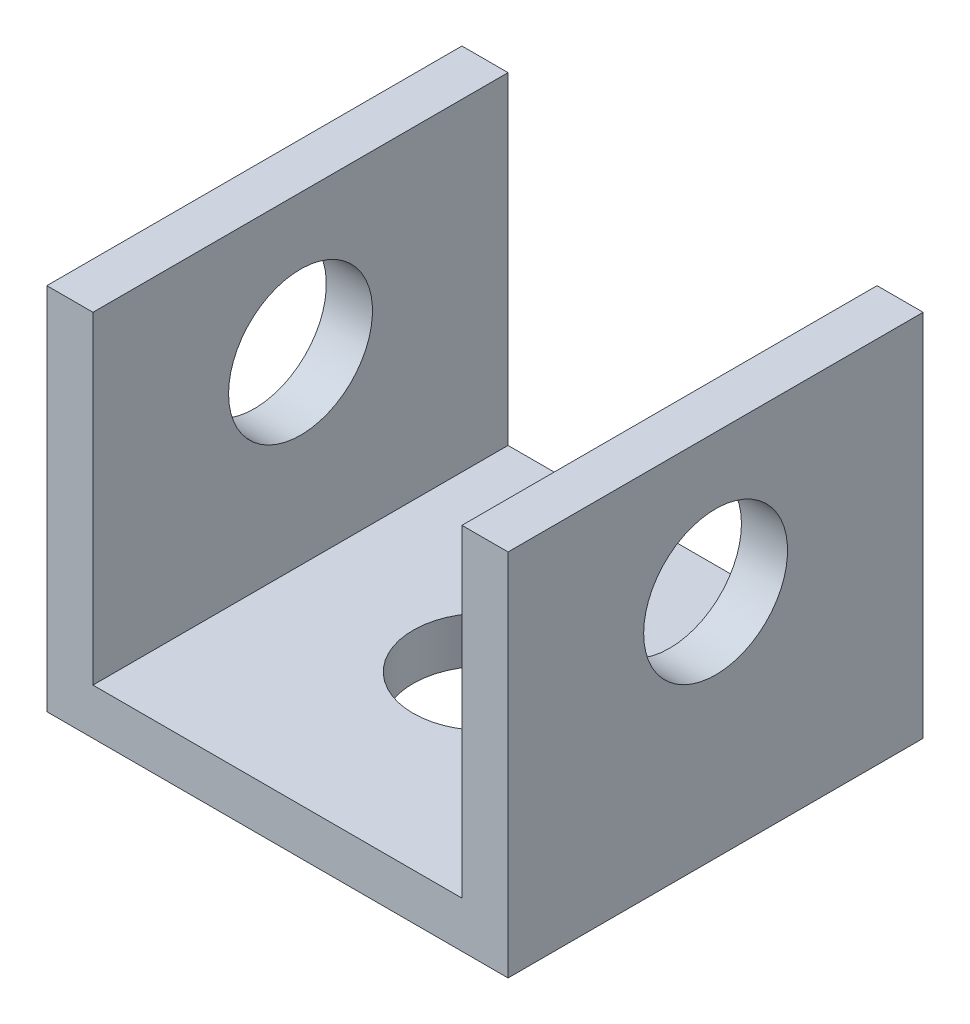
SolidWorks part; units mm, degrees
material "6061 Alloy"
ref_plane "Front Plane" through (0, 0, 0) normal (0, 0, 1) x (1, 0, 0)
ref_plane "Top Plane" through (0, 0, 0) normal (0, 1, 0) x (1, 0, 0)
ref_plane "Right Plane" through (0, 0, 0) normal (1, 0, 0) x (0, 0, -1)
sketch "Sketch1" plane through (0, 0, 0) normal (0, 1, 0) x (1, 0, 0)
  line L1 (25, -22.5) -> (-25, -22.5)
  line L2 (25, -22.5) -> (25, 22.5)
  line L3 (25, 22.5) -> (-25, 22.5)
  line L4 (-25, -22.5) -> (-25, 22.5)
  line L5 (25, -22.5) -> (-25, 22.5) construction
  line L6 (25, 22.5) -> (-25, -22.5) construction
  point P1 (0, 0)
  dimension "50" = 50
  dimension "D2" = 45
extrude "Boss-Extrude1" add sketch "Sketch1" along normal blind 5
sketch "Sketch5" plane through (0, 5, 0) normal (0, 1, 0) x (1, 0, 0)
  line L0 (-25, -22.5) -> (25, -22.5) construction
  line L1 (25, 22.5) -> (20, 22.5)
  line L2 (25, 22.5) -> (25, -22.5)
  line L3 (25, -22.5) -> (20, -22.5)
  line L4 (20, 22.5) -> (20, -22.5)
  line L7 (-25, 22.5) -> (-20, 22.5)
  line L8 (-25, 22.5) -> (-25, -22.5)
  line L9 (-25, -22.5) -> (-20, -22.5)
  line L10 (-20, 22.5) -> (-20, -22.5)
  dimension "D1" = 5
  dimension "D2" = 5
extrude "Boss-Extrude3" add sketch "Sketch5" along normal blind 35
sketch "Sketch9" plane through (0, 5, 0) normal (0, 1, 0) x (1, 0, 0)
  circle A0 centre (0, 0) radius 7.8
extrude "Cut-Extrude5" cut sketch "Sketch9" against normal blind 10
sketch "Sketch11" plane through (-25, 0, 0) normal (-1, 0, 0) x (0, 0, 1)
  line L0 (0, 0) -> (0, 40) construction
  line L5 (-22.5, 0) -> (22.5, 0) construction
  line L6 (-22.5, 40) -> (22.5, 40) construction
  line L7 (0, 40) -> (0, 20) construction
  line L8 (0, 20) -> (0, 30) construction
  line L9 (0, 30) -> (0, 20)
  circle A1 centre (0, 25) radius 7.8
extrude "Cut-Extrude8" cut sketch "Sketch11" against normal through all
